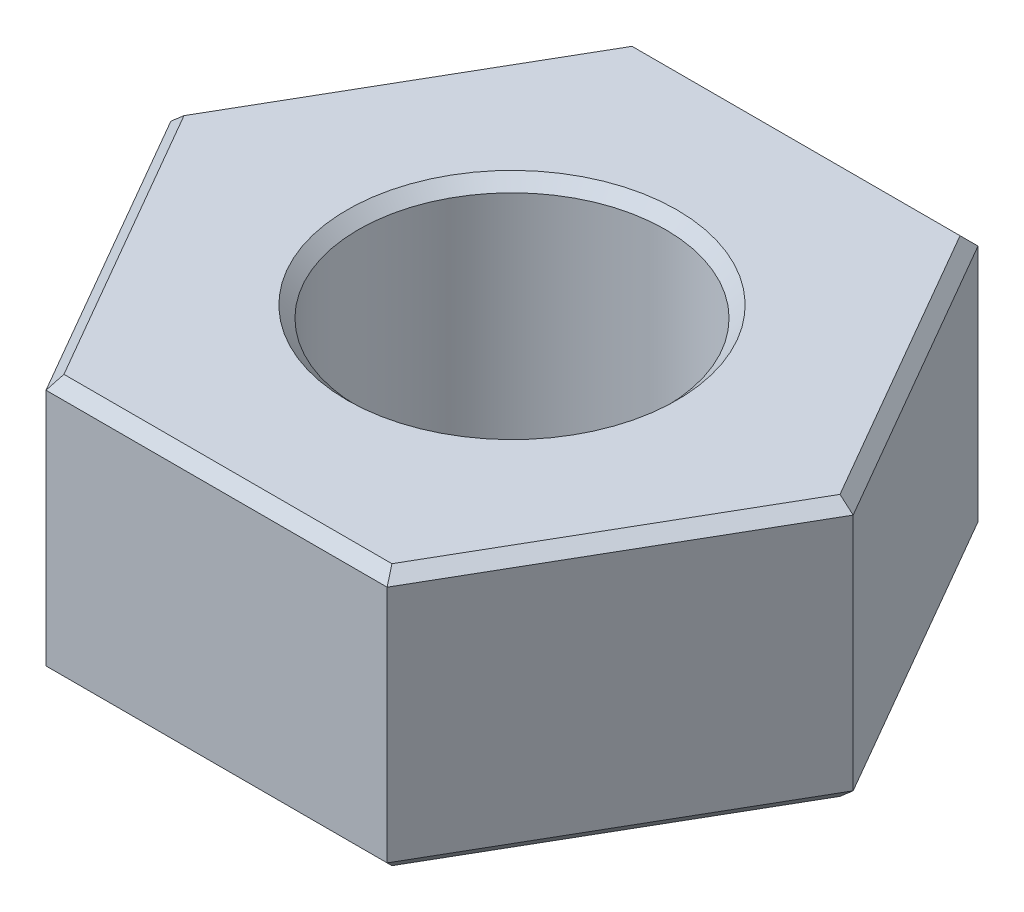
SolidWorks part; units mm, degrees
material "1023 Листовая углеродистая сталь (SS)"
ref_plane "Спереди" through (0, 0, 0) normal (0, 0, 1) x (1, 0, 0)
ref_plane "Сверху" through (0, 0, 0) normal (0, 1, 0) x (1, 0, 0)
ref_plane "Справа" through (0, 0, 0) normal (1, 0, 0) x (0, 0, -1)
sketch "Эскиз1" plane through (0, 0, 0) normal (0, 1, 0) x (1, 0, 0)
  line L1 (3, 0) -> (1.5, 2.5981)
  line L2 (1.5, 2.5981) -> (-1.5, 2.5981)
  line L3 (-1.5, 2.5981) -> (-3, 0)
  line L4 (-3, 0) -> (-1.5, -2.5981)
  line L5 (-1.5, -2.5981) -> (1.5, -2.5981)
  line L6 (1.5, -2.5981) -> (3, 0)
  circle A0 centre (0, 0) radius 2.5981 construction
  circle A1 centre (0, 0) radius 1.35
  dimension "D1" = 2.7
  dimension "D2" = 3
extrude "Бобышка-Вытянуть1" add sketch "Эскиз1" along normal blind 2.3
chamfer "Фаска1" distance 0.1 angle 45 14 edges at (0, 0, 1.35) (2.25, 0, -1.299) (0, 0, -2.5981) (-2.25, 0, -1.299) (-2.25, 0, 1.299) (0, 0, 2.5981) (2.25, 0, 1.299) (0, 2.3, 1.35) (-2.25, 2.3, 1.299) (-2.25, 2.3, -1.299) (0, 2.3, -2.5981) (2.25, 2.3, -1.299) (2.25, 2.3, 1.299) (0, 2.3, 2.5981)
